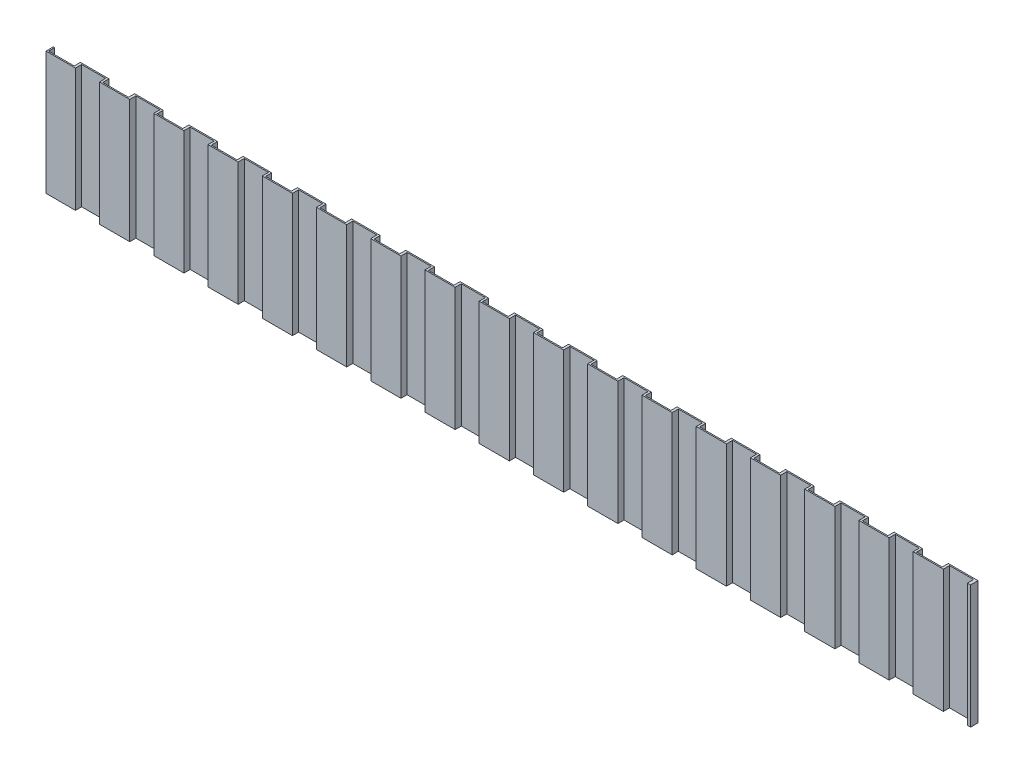
SolidWorks part; units mm, degrees
ref_plane "Front Plane" through (0, 0, 0) normal (0, 0, 1) x (1, 0, 0)
ref_plane "Top Plane" through (0, 0, 0) normal (0, 1, 0) x (1, 0, 0)
ref_plane "Right Plane" through (0, 0, 0) normal (1, 0, 0) x (0, 0, -1)
sketch "Sketch1" plane through (0, 0, 0) normal (0, 0, 1) x (1, 0, 0)
  line L1 (-3750, 2000) -> (3750, 2000)
  line L2 (-3750, 2000) -> (-3750, -2000)
  line L3 (-3750, -2000) -> (3750, -2000)
  line L4 (3750, 2000) -> (3750, -2000)
  line L5 (-3750, 2000) -> (3750, -2000) construction
  line L6 (-3750, -2000) -> (3750, 2000) construction
  point P0 (0, 0)
  dimension "D1" = 7500
  dimension "D2" = 4000
extrude "Boss-Extrude1" add sketch "Sketch1" along normal blind 60
sketch "Sketch2" plane through (0, -2000, 0) normal (0, -1, 0) x (-1, 0, 0)
  line L0 (3750, 0) -> (-3750, 0) construction
  line L1 (3739.0761, 0) -> (3531.0261, 0)
  line L2 (3739.0761, 0) -> (3739.0761, -50)
  line L3 (3739.0761, -50) -> (3531.0261, -50)
  line L4 (3531.0261, 0) -> (3531.0261, -50)
  line L5 (3750, -60) -> (-3750, -60) construction
  line L6 (3510.9951, -60) -> (3315.6922, -60)
  line L7 (3510.9951, -60) -> (3510.9951, -10)
  line L8 (3510.9951, -10) -> (3315.6922, -10)
  line L9 (3315.6922, -60) -> (3315.6922, -10)
  line L10 (3299.0761, -50) -> (3091.0261, -50)
  line L11 (3299.0761, 0) -> (3299.0761, -50)
  line L12 (3299.0761, 0) -> (3091.0261, 0)
  line L13 (3091.0261, 0) -> (3091.0261, -50)
  line L14 (3070.9951, -10) -> (2875.6922, -10)
  line L15 (3070.9951, -60) -> (3070.9951, -10)
  line L16 (3070.9951, -60) -> (2875.6922, -60)
  line L17 (2875.6922, -60) -> (2875.6922, -10)
  line L18 (2859.0761, -50) -> (2651.0261, -50)
  line L19 (2859.0761, 0) -> (2859.0761, -50)
  line L20 (2859.0761, 0) -> (2651.0261, 0)
  line L21 (2651.0261, 0) -> (2651.0261, -50)
  line L22 (2630.9951, -10) -> (2435.6922, -10)
  line L23 (2630.9951, -60) -> (2630.9951, -10)
  line L24 (2630.9951, -60) -> (2435.6922, -60)
  line L25 (2435.6922, -60) -> (2435.6922, -10)
  line L26 (2419.0761, -50) -> (2211.0261, -50)
  line L27 (2419.0761, 0) -> (2419.0761, -50)
  line L28 (2419.0761, 0) -> (2211.0261, 0)
  line L29 (2211.0261, 0) -> (2211.0261, -50)
  line L30 (2190.9951, -10) -> (1995.6922, -10)
  line L31 (2190.9951, -60) -> (2190.9951, -10)
  line L32 (2190.9951, -60) -> (1995.6922, -60)
  line L33 (1995.6922, -60) -> (1995.6922, -10)
  line L34 (1979.0761, -50) -> (1771.0261, -50)
  line L35 (1979.0761, 0) -> (1979.0761, -50)
  line L36 (1979.0761, 0) -> (1771.0261, 0)
  line L37 (1771.0261, 0) -> (1771.0261, -50)
  line L38 (1750.9951, -10) -> (1555.6922, -10)
  line L39 (1750.9951, -60) -> (1750.9951, -10)
  line L40 (1750.9951, -60) -> (1555.6922, -60)
  line L41 (1555.6922, -60) -> (1555.6922, -10)
  line L42 (1539.0761, -50) -> (1331.0261, -50)
  line L43 (1539.0761, 0) -> (1539.0761, -50)
  line L44 (1539.0761, 0) -> (1331.0261, 0)
  line L45 (1331.0261, 0) -> (1331.0261, -50)
  line L46 (1310.9951, -10) -> (1115.6922, -10)
  line L47 (1310.9951, -60) -> (1310.9951, -10)
  line L48 (1310.9951, -60) -> (1115.6922, -60)
  line L49 (1115.6922, -60) -> (1115.6922, -10)
  line L50 (1099.0761, -50) -> (891.0261, -50)
  line L51 (1099.0761, 0) -> (1099.0761, -50)
  line L52 (1099.0761, 0) -> (891.0261, 0)
  line L53 (891.0261, 0) -> (891.0261, -50)
  line L54 (870.9951, -10) -> (675.6922, -10)
  line L55 (870.9951, -60) -> (870.9951, -10)
  line L56 (870.9951, -60) -> (675.6922, -60)
  line L57 (675.6922, -60) -> (675.6922, -10)
  line L58 (659.0761, -50) -> (451.0261, -50)
  line L59 (659.0761, 0) -> (659.0761, -50)
  line L60 (659.0761, 0) -> (451.0261, 0)
  line L61 (451.0261, 0) -> (451.0261, -50)
  line L62 (430.9951, -10) -> (235.6922, -10)
  line L63 (430.9951, -60) -> (430.9951, -10)
  line L64 (430.9951, -60) -> (235.6922, -60)
  line L65 (235.6922, -60) -> (235.6922, -10)
  line L66 (219.0761, -50) -> (11.0261, -50)
  line L67 (219.0761, 0) -> (219.0761, -50)
  line L68 (219.0761, 0) -> (11.0261, 0)
  line L69 (11.0261, 0) -> (11.0261, -50)
  line L70 (-9.0049, -10) -> (-204.3078, -10)
  line L71 (-9.0049, -60) -> (-9.0049, -10)
  line L72 (-9.0049, -60) -> (-204.3078, -60)
  line L73 (-204.3078, -60) -> (-204.3078, -10)
  line L74 (-220.9239, -50) -> (-428.9739, -50)
  line L75 (-220.9239, 0) -> (-220.9239, -50)
  line L76 (-220.9239, 0) -> (-428.9739, 0)
  line L77 (-428.9739, 0) -> (-428.9739, -50)
  line L78 (-449.0049, -10) -> (-644.3078, -10)
  line L79 (-449.0049, -60) -> (-449.0049, -10)
  line L80 (-449.0049, -60) -> (-644.3078, -60)
  line L81 (-644.3078, -60) -> (-644.3078, -10)
  line L82 (-660.9239, -50) -> (-868.9739, -50)
  line L83 (-660.9239, 0) -> (-660.9239, -50)
  line L84 (-660.9239, 0) -> (-868.9739, 0)
  line L85 (-868.9739, 0) -> (-868.9739, -50)
  line L86 (-889.0049, -10) -> (-1084.3078, -10)
  line L87 (-889.0049, -60) -> (-889.0049, -10)
  line L88 (-889.0049, -60) -> (-1084.3078, -60)
  line L89 (-1084.3078, -60) -> (-1084.3078, -10)
  line L90 (-1100.9239, -50) -> (-1308.9739, -50)
  line L91 (-1100.9239, 0) -> (-1100.9239, -50)
  line L92 (-1100.9239, 0) -> (-1308.9739, 0)
  line L93 (-1308.9739, 0) -> (-1308.9739, -50)
  line L94 (-1329.0049, -10) -> (-1524.3078, -10)
  line L95 (-1329.0049, -60) -> (-1329.0049, -10)
  line L96 (-1329.0049, -60) -> (-1524.3078, -60)
  line L97 (-1524.3078, -60) -> (-1524.3078, -10)
  line L98 (-1540.9239, -50) -> (-1748.9739, -50)
  line L99 (-1540.9239, 0) -> (-1540.9239, -50)
  line L100 (-1540.9239, 0) -> (-1748.9739, 0)
  line L101 (-1748.9739, 0) -> (-1748.9739, -50)
  line L102 (-1769.0049, -10) -> (-1964.3078, -10)
  line L103 (-1769.0049, -60) -> (-1769.0049, -10)
  line L104 (-1769.0049, -60) -> (-1964.3078, -60)
  line L105 (-1964.3078, -60) -> (-1964.3078, -10)
  line L106 (-1980.9239, -50) -> (-2188.9739, -50)
  line L107 (-1980.9239, 0) -> (-1980.9239, -50)
  line L108 (-1980.9239, 0) -> (-2188.9739, 0)
  line L109 (-2188.9739, 0) -> (-2188.9739, -50)
  line L110 (-2209.0049, -10) -> (-2404.3078, -10)
  line L111 (-2209.0049, -60) -> (-2209.0049, -10)
  line L112 (-2209.0049, -60) -> (-2404.3078, -60)
  line L113 (-2404.3078, -60) -> (-2404.3078, -10)
  line L114 (-2420.9239, -50) -> (-2628.9739, -50)
  line L115 (-2420.9239, 0) -> (-2420.9239, -50)
  line L116 (-2420.9239, 0) -> (-2628.9739, 0)
  line L117 (-2628.9739, 0) -> (-2628.9739, -50)
  line L118 (-2649.0049, -10) -> (-2844.3078, -10)
  line L119 (-2649.0049, -60) -> (-2649.0049, -10)
  line L120 (-2649.0049, -60) -> (-2844.3078, -60)
  line L121 (-2844.3078, -60) -> (-2844.3078, -10)
  line L122 (-2860.9239, -50) -> (-3068.9739, -50)
  line L123 (-2860.9239, 0) -> (-2860.9239, -50)
  line L124 (-2860.9239, 0) -> (-3068.9739, 0)
  line L125 (-3068.9739, 0) -> (-3068.9739, -50)
  line L126 (-3089.0049, -10) -> (-3284.3078, -10)
  line L127 (-3089.0049, -60) -> (-3089.0049, -10)
  line L128 (-3089.0049, -60) -> (-3284.3078, -60)
  line L129 (-3284.3078, -60) -> (-3284.3078, -10)
  line L130 (-3300.9239, -50) -> (-3508.9739, -50)
  line L131 (-3300.9239, 0) -> (-3300.9239, -50)
  line L132 (-3300.9239, 0) -> (-3508.9739, 0)
  line L133 (-3508.9739, 0) -> (-3508.9739, -50)
  line L134 (-3529.0049, -10) -> (-3724.3078, -10)
  line L135 (-3529.0049, -60) -> (-3529.0049, -10)
  line L136 (-3529.0049, -60) -> (-3724.3078, -60)
  line L137 (-3724.3078, -60) -> (-3724.3078, -10)
  dimension "D1" = 10
  dimension "D2" = 10
  dimension "D3" = 17
extrude "Cut-Extrude1" cut sketch "Sketch2" against normal blind 5107
sketch "Sketch3" plane through (0, 0, 60) normal (0, 0, 1) x (1, 0, 0)
  line L0 (-3750, 2000) -> (-3750, -2000) construction
  line L1 (-3750, 0) -> (4446.8689, 0)
  line L2 (-3750, 0) -> (-3750, -2618.2151)
  line L3 (-3750, -2618.2151) -> (4446.8689, -2618.2151)
  line L4 (4446.8689, 0) -> (4446.8689, -2618.2151)
extrude "Cut-Extrude2" cut sketch "Sketch3" against normal blind 1189.716
sketch "Sketch4" plane through (0, 0, 60) normal (0, 0, 1) x (1, 0, 0)
  line L0 (-3750, 2000) -> (-3750, 0) construction
  line L1 (-3750, 1000) -> (4860.4204, 1000)
  line L2 (-3750, 1000) -> (-3750, -1020.7543)
  line L3 (-3750, -1020.7543) -> (4860.4204, -1020.7543)
  line L4 (4860.4204, 1000) -> (4860.4204, -1020.7543)
extrude "Cut-Extrude3" cut sketch "Sketch4" against normal blind 1189.716
